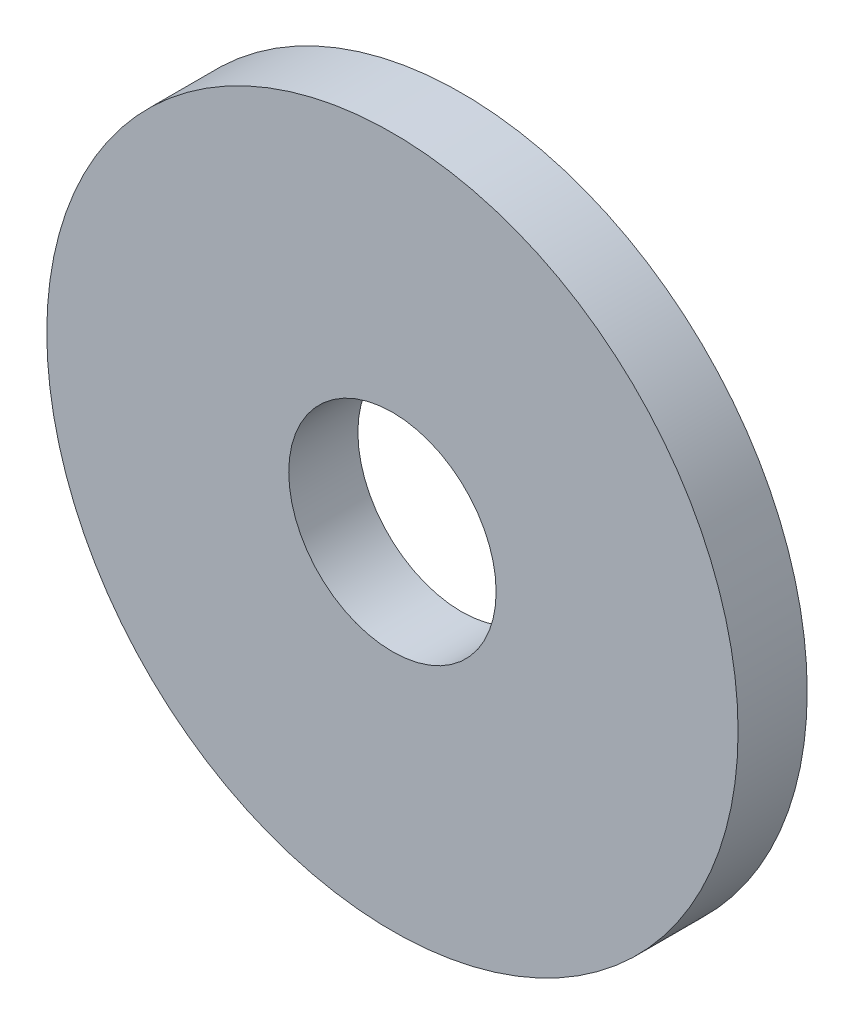
SolidWorks part; units mm, degrees
ref_plane "Plan de face" through (0, 0, 0) normal (0, 0, 1) x (1, 0, 0)
ref_plane "Plan de dessus" through (0, 0, 0) normal (0, 1, 0) x (1, 0, 0)
ref_plane "Plan de droite" through (0, 0, 0) normal (1, 0, 0) x (0, 0, -1)
sketch "Esquisse1" plane through (0, 0, 0) normal (0, 0, 1) x (1, 0, 0)
  circle A0 centre (0, 0) radius 5
  circle A1 centre (0, 0) radius 1.5
  dimension "D1" = 3
  dimension "D2" = 10
extrude "Boss.-Extru.1" add sketch "Esquisse1" along normal blind 1
